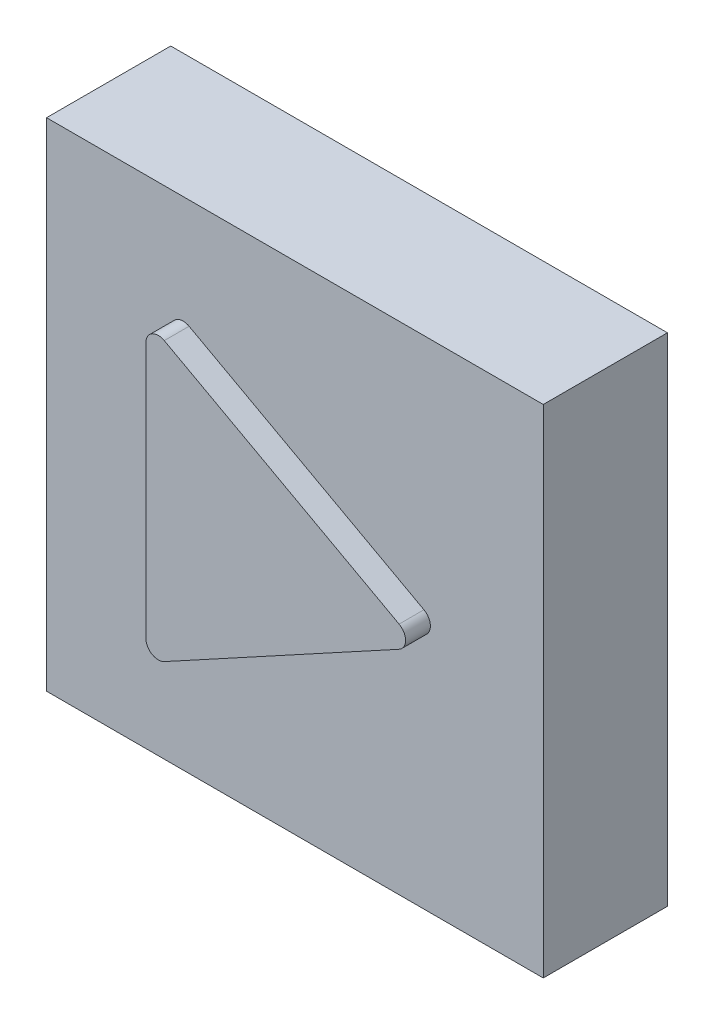
SolidWorks part; units mm, degrees
ref_plane "Front Plane" through (0, 0, 0) normal (0, 0, 1) x (1, 0, 0)
ref_plane "Top Plane" through (0, 0, 0) normal (0, 1, 0) x (1, 0, 0)
ref_plane "Right Plane" through (0, 0, 0) normal (1, 0, 0) x (0, 0, -1)
sketch "Sketch1" plane through (0, 0, 0) normal (0, 0, 1) x (1, 0, 0)
  line L1 (-10, -10) -> (10, -10)
  line L2 (-10, -10) -> (-10, 10)
  line L3 (-10, 10) -> (10, 10)
  line L4 (10, -10) -> (10, 10)
  line L5 (-10, -10) -> (10, 10) construction
  line L6 (-10, 10) -> (10, -10) construction
  point P0 (0, 0)
extrude "Boss-Extrude1" add sketch "Sketch1" along normal blind 5
ref_plane "Plane1" through (0, 0, 5) normal (0, 0, 1) x (1, 0, 0)
sketch "Sketch2" plane through (0, 0, 5) normal (0, 0, 1) x (1, 0, 0)
  line L0 (-5, 5.1577) -> (-5, -5.1577)
  line L1 (-4.2606, -5.5967) -> (5.1953, -0.4389)
  line L2 (5.1953, 0.4389) -> (-4.2606, 5.5967)
  arc A0 (-5, -5.1577) -> (-4.2606, -5.5967) centre (-4.5, -5.1577) ccw
  arc A1 (5.1953, -0.4389) -> (5.1953, 0.4389) centre (4.9558, 0) ccw
  arc A2 (-5, 5.1577) -> (-4.2606, 5.5967) centre (-4.5, 5.1577) cw
  dimension "D1" = 0.5
sketch "Sketch4" plane through (0, 0, 5) normal (0, 0, 1) x (1, 0, 0)
  line L1 (-3, 1) -> (2, 1)
  line L2 (-3, 1) -> (-3, -1)
  line L3 (-3, -1) -> (2, -1)
  line L4 (2, 1) -> (2, -1)
sketch "Sketch6" plane through (0, 0, 5) normal (0, 0, 1) x (1, 0, 0)
  circle A0 centre (0, 0) radius 0.6
  circle A1 centre (0, 0) radius 1
extrude "Cut-Extrude1" cut sketch "Sketch6" against normal blind 5 contours A0
extrude "Boss-Extrude2" add sketch "Sketch2" along normal blind 1
